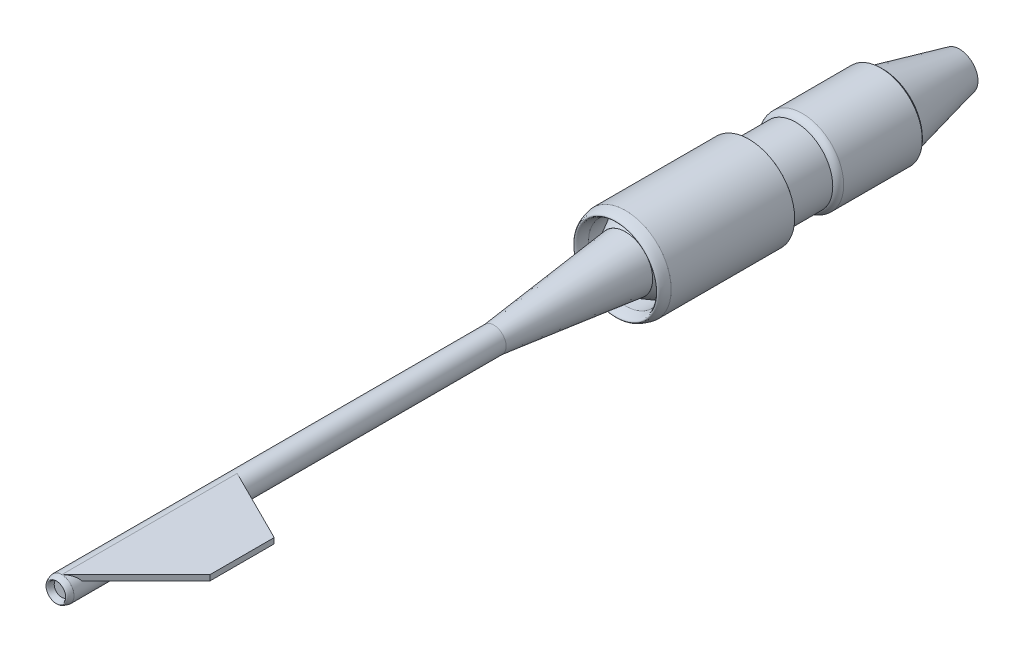
SolidWorks part; units mm, degrees
ref_plane "Front Plane" through (0, 0, 0) normal (0, 0, 1) x (1, 0, 0)
ref_plane "Top Plane" through (0, 0, 0) normal (0, 1, 0) x (1, 0, 0)
ref_plane "Right Plane" through (0, 0, 0) normal (1, 0, 0) x (0, 0, -1)
sketch "Sketch1" plane through (0, 0, 0) normal (0, 0, 1) x (1, 0, 0)
  circle A0 centre (0, 0) radius 416.25
  circle A1 centre (0, 0) radius 337.5
extrude "Boss-Extrude1" add sketch "Sketch1" against normal blind 1125
sketch "Sketch2" plane through (0, 0, 0) normal (1, 0, 0) x (0, 0, -1)
  line L0 (0, 416.25) -> (0, 337.5) construction
  line L1 (0, 337.5) -> (0, 376.875) construction
  line L2 (0, 376.875) -> (-90, 376.875) construction
  line L3 (0, 416.25) -> (0, 337.5)
  line L4 (0, 0) -> (98.8797, 0) construction
  spline S0 degree 2 poles (0, 337.5) (-180, 376.875) (0, 416.25) knots 0 0 0 1 1 1
revolve "Revolve1" add sketch "Sketch2" angle 360 about L4
ref_plane "Plane1" through (0, 0, 0) normal (0, 0, 1) x (1, 0, 0)
sketch "Sketch3" plane through (0, 0, 0) normal (0, 0, 1) x (1, 0, 0)
  circle A0 centre (0, 0) radius 247.5
sketch "Sketch4" plane through (0, 0, 0) normal (0, 1, 0) x (1, 0, 0)
  line L0 (0, 0) -> (0, -1200)
  line L1 (0, -1200) -> (112.5, -1200)
  line L2 (0, 0) -> (247.5, 0)
  line L3 (-247.5, 0) -> (247.5, 0) construction
  line L4 (-457.875, 0) -> (457.875, 0) construction
  line L5 (247.5, 0) -> (112.5, -1200)
revolve "Revolve2" add sketch "Sketch4" angle 360 about L0
sketch "Sketch5" plane through (0, 0, 1200) normal (0, 0, 1) x (1, 0, 0)
  circle A0 centre (0, 0) radius 112.5
extrude "Boss-Extrude2" add sketch "Sketch5" along normal blind 3937.5
sketch "Sketch14" plane through (0, 0, 0) normal (1, 0, 0) x (0, 0, -1)
  line L0 (-5137.5, 112.5) -> (-5137.5, 67.5)
  line L1 (-5137.5, 112.5) -> (-5137.5, -112.5) construction
  line L2 (-5137.5, 67.5) -> (-5137.5, 90)
  line L3 (-5137.5, 90) -> (-5187.5, 90) construction
  line L4 (-5137.5, 0) -> (-5198.2274, 0) construction
  line L5 (-5137.5, 112.5) -> (-5137.5, -112.5) construction
  spline S0 degree 2 poles (-5137.5, 67.5) (-5237.5, 90) (-5137.5, 112.5) knots 0 0 0 1 1 1
  dimension "D1" = 50
  dimension "D2" = 67.5
  dimension "D3" = 90
revolve "Revolve4" add sketch "Sketch14" angle 360 about L4
sketch "Sketch15" plane through (0, 0, -1125) normal (0, 0, -1) x (-1, 0, 0)
  circle A0 centre (0, 0) radius 337.5
extrude "Boss-Extrude5" add sketch "Sketch15" along normal blind 486 separate body
sketch "Sketch16" plane through (0, 0, -1611) normal (0, 0, -1) x (-1, 0, 0)
  line L0 (0, 337.5) -> (0, 416.25) construction
  line L1 (0, 376.875) -> (79.8334, 376.875) construction
  circle A0 centre (0, 0) radius 337.5 construction
  circle A1 centre (0, 0) radius 337.5 construction
  circle A2 centre (0, 0) radius 416.25 construction
  circle A4 centre (0, 0) radius 376.875
extrude "Boss-Extrude6" add sketch "Sketch16" along normal blind 716
sketch "Sketch17" plane through (0, 0, 0) normal (1, 0, 0) x (0, 0, -1)
  line L0 (2327, 0) -> (3043, 0)
  line L1 (2327, -376.875) -> (2327, 376.875) construction
  line L2 (3043, 0) -> (3043, 168.75)
  line L3 (1611, 337.5) -> (2327, 337.5) construction
  line L4 (2327, 0) -> (2327, 337.5)
  line L5 (2327, 337.5) -> (3043, 168.75)
revolve "Revolve5" add sketch "Sketch17" angle 360 about L0
sketch "Sketch18" plane through (0, 0, 0) normal (1, 0, 0) x (0, 0, -1)
  line L0 (0, 247.5) -> (306.6324, 416.25)
  line L1 (1125, 416.25) -> (0, 416.25) construction
  line L2 (0, 247.5) -> (306.6324, 247.5)
  line L3 (306.6324, 247.5) -> (306.6324, 416.25)
  line L4 (0, 0) -> (306.6324, 0) construction
revolve "Revolve6" add sketch "Sketch18" angle 360 about L4
sketch "Sketch19" plane through (0, 0, 0) normal (1, 0, 0) x (0, 0, -1)
  line L1 (1611, 337.5) -> (1611, -337.5) construction
  line L2 (1611, 0) -> (1611, 337.5) construction
  line L3 (1611, 337.5) -> (1551, 337.5)
  line L4 (1611, 0) -> (1571, 0) construction
  line L5 (1611, 337.5) -> (1125, 337.5) construction
  line L6 (1611, 337.5) -> (1611, 376.875)
  line L7 (1611, 376.875) -> (1611, -376.875) construction
  arc A0 (1551, 337.5) -> (1611, 376.875) centre (1614.9642, 305.4325) cw
revolve "Revolve9" add sketch "Sketch19" angle 360 about L4
sketch "Sketch20" plane through (0, 0, 0) normal (1, 0, 0) x (0, 0, -1)
  line L0 (1125, 337.5) -> (1125, 416.25)
  line L1 (1125, 337.5) -> (1155, 337.5)
  line L2 (1551, 337.5) -> (1125, 337.5) construction
  line L3 (1125, 0) -> (1175, 0) construction
  line L4 (1125, -416.25) -> (1125, 416.25) construction
  conic Q0 (1155, 337.5) -> (1125, 416.25) control (1155, 382.5893) rho 0.44632
revolve "Revolve11" add sketch "Sketch20" angle 360 about L3
sketch "Sketch21" plane through (0, 0, 0) normal (1, 0, 0) x (0, 0, -1)
  line L0 (2327, 337.5) -> (2327, 376.875)
  line L1 (2327, 0) -> (2377, 0) construction
  line L2 (2327, -376.875) -> (2327, 376.875) construction
  line L3 (2327, 337.5) -> (2356.2, 330.618)
  line L4 (3043, 168.75) -> (2327, 337.5) construction
  conic Q0 (2327, 376.875) -> (2356.2, 330.618) control (2356.2, 357.1875) rho 0.453502
revolve "Revolve12" add sketch "Sketch21" angle 360 about L1
sketch3d "3DSketch1"
  line L0 (1.7689, 112.4861, 5137.5) -> (-673.2311, 112.4861, 5137.5) construction
  circle A0 centre (0, 0, 5137.5) radius 112.5 construction
  point P2 (0, 0, 5250)
ref_plane "Plane2" through (0, 112.4861, 0) normal (0, 1, 0) x (1, 0, 0)
sketch "Sketch22" plane through (0, 112.4861, 0) normal (0, 1, 0) x (1, 0, 0)
  line L0 (1.7689, -5137.5) -> (1.7689, -3540)
  line L1 (-673.2311, -5137.5) -> (-673.2311, -4462.5) construction
  line L2 (-673.2311, -4462.5) -> (1.7689, -4462.5) construction
  line L3 (-673.2311, -4462.5) -> (1.7689, -5137.5)
  line L4 (-673.2311, -4462.5) -> (-673.2311, -3877.5)
  line L5 (-673.2311, -3877.5) -> (1.7689, -3540)
  line L6 (676.7689, -3877.5) -> (1.7689, -3540)
  line L7 (676.7689, -4462.5) -> (1.7689, -5137.5)
  line L8 (676.7689, -4462.5) -> (676.7689, -3877.5)
extrude "Boss-Extrude7" add sketch "Sketch22" against normal blind 50 contours L7 L8 L6 L0
sketch3d "3DSketch2"
  line L0 (0, 0, 0) -> (-416.25, 0, 0)
  line L1 (-416.25, 0, 0) -> (-416.25, 0, -1125)
  line L2 (0, 0, 0) -> (-409.9262, -72.2811, 0)
  line L3 (-409.9262, -72.2811, 0) -> (-416.438, -35.3508, 0)
  line L4 (-409.9262, -72.2811, 0) -> (-403.4144, -109.2113, 0)
  line L5 (0, 0, 0) -> (416.25, 0, 0)
  line L6 (416.25, 0, 0) -> (416.25, -37.5, 0)
  line L7 (416.25, 0, 0) -> (416.25, 37.5, 0)
  circle A1 centre (0, 0, 0) radius 416.25 construction
  circle A3 centre (0, 0, -1125) radius 416.25 construction
  arc A4 (-416.25, 0, 0) -> (-409.9262, -72.2811, 0) centre (0, 0, 0) ccw
  point P5 (0, 0, 416.25)
  point P10 (0, 0, -708.75)
  point P12 (0, 0, 416.25)
  dimension "D1" = 90
  dimension "D2" = 90
  dimension "D3" = 90
